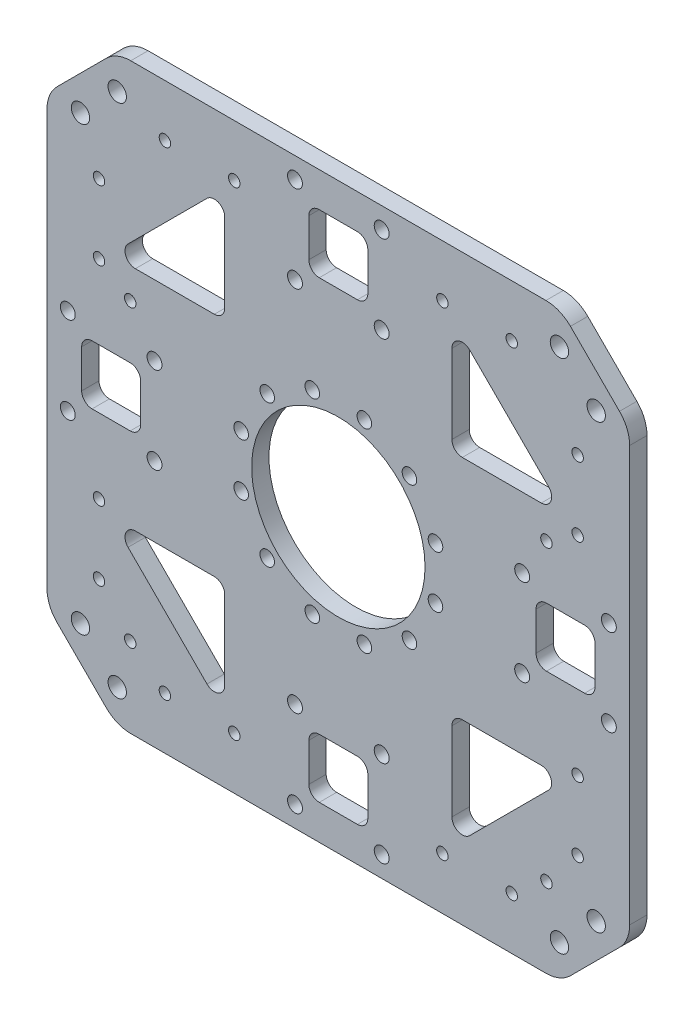
SolidWorks part; units mm, degrees
material "Hexcel AS4C (3000 丝)"
ref_plane "前视基准面" through (0, 0, 0) normal (0, 0, 1) x (1, 0, 0)
ref_plane "上视基准面" through (0, 0, 0) normal (0, 1, 0) x (1, 0, 0)
ref_plane "右视基准面" through (0, 0, 0) normal (1, 0, 0) x (0, 0, -1)
sketch "草图1" plane through (0, 0, 0) normal (0, 0, 1) x (1, 0, 0)
  line L0 (-84, 84) -> (-84, -84)
  line L1 (-64.3467, 64.3467) -> (64.3467, 64.3467) construction
  line L2 (-64.3467, 64.3467) -> (-64.3467, -64.3467) construction
  line L3 (-64.3467, -64.3467) -> (64.3467, -64.3467) construction
  line L4 (64.3467, 64.3467) -> (64.3467, -64.3467) construction
  line L5 (-64.3467, 64.3467) -> (64.3467, -64.3467) construction
  line L6 (-64.3467, -64.3467) -> (64.3467, 64.3467) construction
  line L7 (-84, -84) -> (84, -84)
  line L8 (84, 84) -> (84, -84)
  line L9 (-84, 84) -> (84, 84)
  circle A0 centre (0, 0) radius 91 construction
  dimension "D1" = 182
  dimension "D2" = 168
extrude "凸台-拉伸1" add sketch "草图1" along normal blind 5
sketch "草图2" plane through (0, 0, 5) normal (0, 0, 1) x (1, 0, 0)
  line L0 (64, 84) -> (84, 64)
  line L1 (84, 84) -> (-84, 84) construction
  line L2 (84, -84) -> (84, 84) construction
  line L3 (84, 64) -> (84, 84)
  line L4 (84, 84) -> (64, 84)
  line L5 (64, -84) -> (84, -84)
  line L6 (84, -84) -> (84, -64)
  line L7 (84, -64) -> (64, -84)
  line L8 (-84, -64) -> (-84, -84)
  line L9 (-84, -84) -> (-64, -84)
  line L10 (-64, -84) -> (-84, -64)
  line L11 (-64, 84) -> (-84, 84)
  line L12 (-84, 84) -> (-84, 64)
  line L13 (-84, 64) -> (-64, 84)
  circle A0 centre (0, 0) radius 91 construction
  point P23 (0, 0)
  dimension "D1" = 182
  dimension "D2" = 20
  dimension "D3" = 4
extrude "切除-拉伸1" cut sketch "草图2" against normal through all
sketch "草图3" plane through (0, 0, 5) normal (0, 0, 1) x (1, 0, 0)
  line L0 (0, 0) -> (0, 25) construction
  line L1 (0, 0) -> (10.2555, 38.2742) construction
  circle A0 centre (0, 0) radius 29 construction
  circle A1 centre (7.5058, 28.0118) radius 2.1
  circle A2 centre (0, 0) radius 25
  dimension "D1" = 58
  dimension "D2" = 4.2
  dimension "D3" = 50
  dimension "D4" = 15
extrude "切除-拉伸2" cut sketch "草图3" against normal through all
sketch "草图4" plane through (0, 0, 0) normal (0, 0, -1) x (-1, 0, 0)
  line L0 (-84, 0) -> (84, 0) construction
  line L1 (-84, -64) -> (-84, 64) construction
  line L2 (84, 64) -> (84, -64) construction
  line L3 (0, 84) -> (0, -84) construction
  line L4 (-64, 84) -> (64, 84) construction
  line L5 (64, -84) -> (-64, -84) construction
  circle A0 centre (64, 0) radius 2.15
  circle A1 centre (74, 0) radius 2.15
  circle A2 centre (54, 0) radius 2.15
  circle A3 centre (0, -54) radius 2.15
  circle A4 centre (0, -64) radius 2.15
  circle A5 centre (0, -74) radius 2.15
  circle A6 centre (-54, 0) radius 2.15
  circle A7 centre (-64, 0) radius 2.15
  circle A8 centre (-74, 0) radius 2.15
  circle A9 centre (0, 54) radius 2.15
  circle A10 centre (0, 64) radius 2.15
  circle A11 centre (0, 74) radius 2.15
  point P39 (0, 0)
  dimension "D1" = 4.3
  dimension "D2" = 10
  dimension "D3" = 10
  dimension "D4" = 10
  dimension "D5" = 4
extrude "切除-拉伸3" [suppressed] cut sketch "草图4" against normal through all
pattern_circular "阵列(圆周)1" count 12 over 360 about axis through (0, 0, 0) along (0, 0, 1) of "切除-拉伸2"
sketch "草图5" plane through (0, 0, 0) normal (0, 0, -1) x (-1, 0, 0)
  line L0 (54.1005, 84) -> (84, 54.1005) construction
  line L1 (-64, 84) -> (64, 84) construction
  line L2 (84, 64) -> (84, -64) construction
  line L3 (84, 64) -> (64, 84) construction
  line L4 (69.0503, 69.0503) -> (91.3677, 91.3677) construction
  circle A0 centre (63.747, 74.3536) radius 2.65
  circle A1 centre (69.0503, 69.0503) radius 2.65 construction
  circle A2 centre (74.3536, 63.747) radius 2.65
  dimension "D2" = 15
  dimension "D3" = 5.3
  dimension "D1" = 7
extrude "切除-拉伸4" cut sketch "草图5" against normal through all
pattern_circular "阵列(圆周)2" count 4 over 360 about axis through (0, 0, 0) along (0, 0, 1) of "切除-拉伸4"
fillet "圆角1" radius 10 8 edges at (64, 84, 2.5) (84, 64, 2.5) (84, -64, 2.5) (64, -84, 2.5) (-64, -84, 2.5) (-84, -64, 2.5) (-84, 64, 2.5) (-64, 84, 2.5)
sketch "草图6" plane through (0, 0, 0) normal (0, 0, -1) x (-1, 0, 0)
  line L0 (0, 84) -> (0, -84) construction
  line L1 (-59.8579, 84) -> (59.8579, 84) construction
  line L2 (59.8579, -84) -> (-59.8579, -84) construction
  line L3 (-84, 0) -> (84, 0) construction
  line L4 (-84, -59.8579) -> (-84, 59.8579) construction
  line L5 (84, 59.8579) -> (84, -59.8579) construction
  line L6 (-8.5, 71) -> (-8.5, 60)
  line L7 (-12.5, 78) -> (12.5, 78) construction
  line L8 (-12.5, 78) -> (-12.5, 53) construction
  line L9 (-12.5, 53) -> (12.5, 53) construction
  line L10 (12.5, 78) -> (12.5, 53) construction
  line L11 (-12.5, 78) -> (12.5, 53) construction
  line L12 (-12.5, 53) -> (12.5, 78) construction
  line L13 (-5.5, 57) -> (5.5, 57)
  line L14 (8.5, 71) -> (8.5, 60)
  line L15 (-5.5, 74) -> (5.5, 74)
  line L16 (-8.5, 57) -> (8.5, 57) construction
  line L17 (8.5, 74) -> (8.5, 57) construction
  line L18 (-8.5, 74) -> (8.5, 74) construction
  line L19 (-8.5, 74) -> (-8.5, 57) construction
  circle A0 centre (-12.5, 78) radius 2.15
  circle A1 centre (12.5, 78) radius 2.15
  circle A2 centre (12.5, 53) radius 2.15
  circle A3 centre (-12.5, 53) radius 2.15
  arc A4 (5.5, 57) -> (8.5, 60) centre (5.5, 60) ccw
  arc A5 (8.5, 71) -> (5.5, 74) centre (5.5, 71) ccw
  arc A6 (-8.5, 71) -> (-5.5, 74) centre (-5.5, 71) cw
  arc A7 (-8.5, 60) -> (-5.5, 57) centre (-5.5, 60) ccw
  point P12 (0, 65.5)
  dimension "D4" = 4.3
  dimension "D6" = 3
  dimension "D1" = 25
  dimension "D2" = 25
  dimension "D3" = 6
  dimension "D5" = 4
extrude "切除-拉伸5" cut sketch "草图6" against normal through all
pattern_circular "阵列(圆周)3" count 4 over 360 about axis through (0, 0, 0) along (0, 0, 1) of "切除-拉伸5"
sketch "草图7" plane through (0, 0, 0) normal (0, 0, -1) x (-1, 0, 0)
  line L0 (0, 84) -> (0, -84) construction
  line L3 (-59.8579, 84) -> (59.8579, 84) construction
  line L4 (-60, 24) -> (60, 24) construction
  line L5 (-60, 24) -> (-60, -61) construction
  line L6 (-60, -61) -> (60, -61) construction
  line L7 (60, 24) -> (60, -61) construction
  line L8 (-60, 24) -> (60, -61) construction
  line L9 (-60, -61) -> (60, 24) construction
  line L10 (59.8579, -84) -> (-59.8579, -84) construction
  circle A0 centre (60, 24) radius 1.65
  circle A1 centre (-60, 24) radius 1.65
  circle A2 centre (-60, -61) radius 1.65
  circle A3 centre (60, -61) radius 1.65
  point P6 (0, -18.5)
  dimension "D3" = 3.3
  dimension "D1" = 85
  dimension "D2" = 120
  dimension "D4" = 60
extrude "切除-拉伸6" cut sketch "草图7" against normal through all
sketch "草图8" plane through (0, 0, 0) normal (0, 0, -1) x (-1, 0, 0)
  line L0 (-74, 0) -> (-57, 0) construction
  line L1 (-74, 5.5) -> (-74, -5.5) construction
  line L2 (-57, -5.5) -> (-57, 5.5) construction
  line L3 (0, 74) -> (0, 57) construction
  line L4 (74, 0) -> (57, 0) construction
  line L5 (0, -74) -> (0, -57) construction
  line L6 (-65.5, 0) -> (0, 65.5) construction
  line L7 (0, 65.5) -> (65.5, 0) construction
  line L8 (65.5, 0) -> (0, -65.5) construction
  line L9 (0, -65.5) -> (-65.5, 0) construction
  line L10 (32.75, 32.75) -> (32.75, 65.7525)
  line L11 (32.75, 65.7525) -> (65.7525, 32.75)
  line L12 (65.7525, 32.75) -> (32.75, 32.75)
  line L13 (32.75, 32.75) -> (93.9198, 93.9198) construction
  line L14 (81.0711, 66.9289) -> (66.9289, 81.0711) construction
  point P15 (0, 0)
  dimension "D2" = 35
  dimension "D1" = 4
extrude "切除-拉伸7" cut sketch "草图8" against normal through all
pattern_circular "阵列(圆周)4" count 4 over 360 about axis through (0, 0, 0) along (0, 0, 1) of "切除-拉伸7"
fillet "圆角2" radius 3 12 edges at (65.7525, -32.75, 2.5) (32.75, -32.75, 2.5) (32.75, -65.7525, 2.5) (-32.75, -65.7525, 2.5) (-32.75, -32.75, 2.5) (-65.7525, -32.75, 2.5) (-65.7525, 32.75, 2.5) (-32.75, 65.7525, 2.5) (-32.75, 32.75, 2.5) (32.75, 32.75, 2.5) (65.7525, 32.75, 2.5) (32.75, 65.7525, 2.5)
sketch "草图9" plane through (0, 0, 0) normal (0, 0, -1) x (-1, 0, 0)
  line L0 (-79.9573, 69) -> (106.0467, 69) construction
  line L1 (0, 0) -> (0, 147.231) construction
  line L2 (-59.8579, 84) -> (59.8579, 84) construction
  line L3 (0, 0) -> (104.0072, 0) construction
  circle A0 centre (-50, 69) radius 1.65
  circle A1 centre (-30, 69) radius 1.65
  circle A2 centre (30, 69) radius 1.65
  circle A3 centre (50, 69) radius 1.65
  circle A4 centre (69, 30) radius 1.65
  circle A5 centre (69, 50) radius 1.65
  circle A6 centre (69, -30) radius 1.65
  circle A7 centre (69, -50) radius 1.65
  circle A8 centre (30, -69) radius 1.65 [skipped]
  circle A9 centre (50, -69) radius 1.65 [skipped]
  circle A10 centre (-30, -69) radius 1.65 [skipped]
  circle A11 centre (-50, -69) radius 1.65 [skipped]
  circle A12 centre (-69, -30) radius 1.65
  circle A13 centre (-69, -50) radius 1.65
  circle A14 centre (-69, 30) radius 1.65
  circle A15 centre (-69, 50) radius 1.65
  circle A16 centre (-30, -69) radius 1.65
  circle A17 centre (-50, -69) radius 1.65
  circle A18 centre (30, -69) radius 1.65
  circle A19 centre (50, -69) radius 1.65
  point P42 (0, 0)
  dimension "D1" = 3.3
  dimension "D2" = 20
  dimension "D3" = 30
  dimension "D4" = 15
  dimension "D5" = 4
extrude "切除-拉伸8" cut sketch "草图9" against normal through all
